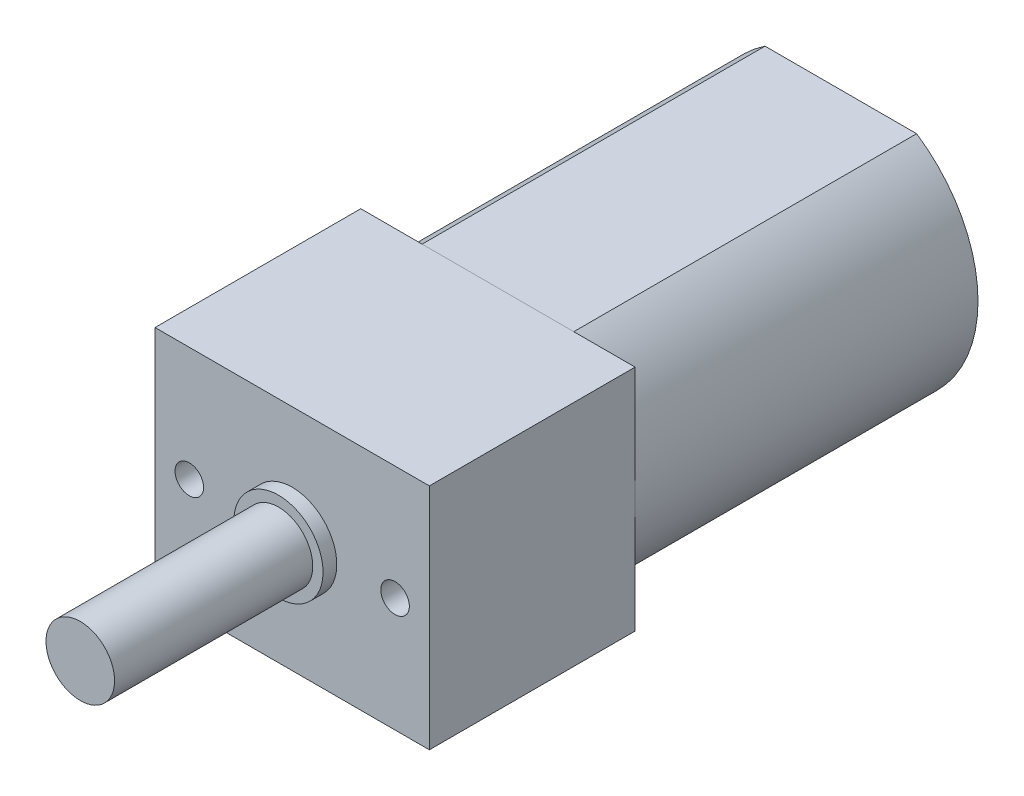
SolidWorks part; units mm, degrees
ref_plane "Front Plane" through (0, 0, 0) normal (0, 0, 1) x (1, 0, 0)
ref_plane "Top Plane" through (0, 0, 0) normal (0, 1, 0) x (1, 0, 0)
ref_plane "Right Plane" through (0, 0, 0) normal (1, 0, 0) x (0, 0, -1)
sketch "Sketch1" plane through (0, 0, 0) normal (0, 0, 1) x (1, 0, 0)
  line L1 (-6, -5) -> (6, -5)
  line L2 (-6, -5) -> (-6, 5)
  line L3 (-6, 5) -> (6, 5)
  line L4 (6, -5) -> (6, 5)
  line L5 (-6, -5) -> (6, 5) construction
  line L6 (-6, 5) -> (6, -5) construction
  point P0 (0, 0)
  dimension "D1" = 12
  dimension "D2" = 10
extrude "Boss-Extrude1" add sketch "Sketch1" along normal blind 9
sketch "Sketch2" plane through (0, 0, 0) normal (1, 0, 0) x (0, 0, -1)
  line L0 (-9, 0) -> (-9, 1.95)
  line L1 (-9, -5) -> (-9, 5) construction
  line L2 (-9, 1.95) -> (-9.6, 1.95)
  line L3 (-9.6, 1.95) -> (-9.6, 1.5)
  line L4 (-9.6, 1.5) -> (-18.27, 1.5)
  line L5 (-18.27, 1.5) -> (-18.27, 0)
  line L7 (-9, 0) -> (-18.27, 0)
  dimension "D1" = 1.5
  dimension "D2" = 1.95
  dimension "D3" = 0.6
  dimension "D4" = 9.27
revolve "Revolve1" add sketch "Sketch2" angle 360 about L7
sketch "Sketch3" plane through (0, 0, 0) normal (0, 0, -1) x (-1, 0, 0)
  line L0 (6, 5) -> (6, -5) construction
  line L1 (-3.3166, 5) -> (3.3166, 5)
  line L2 (-6, 5) -> (6, 5) construction
  line L3 (-3.3166, -5) -> (3.3166, -5)
  line L4 (6, -5) -> (-6, -5) construction
  arc A0 (-3.3166, 5) -> (-3.3166, -5) centre (0, 0) ccw
  arc A1 (3.3166, -5) -> (3.3166, 5) centre (0, 0) ccw
extrude "Boss-Extrude2" add sketch "Sketch3" along normal blind 15 separate body
sketch "Sketch4" plane through (0, 0, -15) normal (0, 0, -1) x (-1, 0, 0)
  circle A0 centre (0, 0) radius 2.5
  dimension "D1" = 5
extrude "Boss-Extrude3" add sketch "Sketch4" along normal blind 2
hole_wizard "M1.6x0.35 Tapped Hole1" positions "Sketch6" profile "Sketch5" tap size "M1.6x0.35" standard "ANSI Metric"
sketch "Sketch6" plane through (0, 0, 9) normal (0, 0, 1) x (1, 0, 0)
  line L0 (0, 0) -> (0, 3.6334) construction
  point P2 (-4.5, 0)
  point P14 (4.5, 0)
  dimension "D1" = 4.5
sketch "Sketch5" plane through (-4.5, 0, 9) normal (1, 0, 0) x (0, -1, 0)
  line L0 (0, 0) -> (0, 2.4255)
  line L1 (0, 2.4255) -> (0.625, 2.05)
  line L2 (0.625, 2.05) -> (0.625, 0)
  line L5 (0.625, 0) -> (0, 0)
  line L10 (0, 2.4255) -> (-0.625, 2.05) construction
  line L11 (0, -6.35) -> (0, 107.95) construction
  dimension "Tap Drill Dia." = 1.25
  dimension "Tap Drill Depth" = 2.05
  dimension "Drill Angle" = 118
cosmetic thread "Hole Thread1" parameters "D1"=1, "D2"=1.6
cosmetic thread "Hole Thread2" parameters "D1"=1, "D2"=1.6
